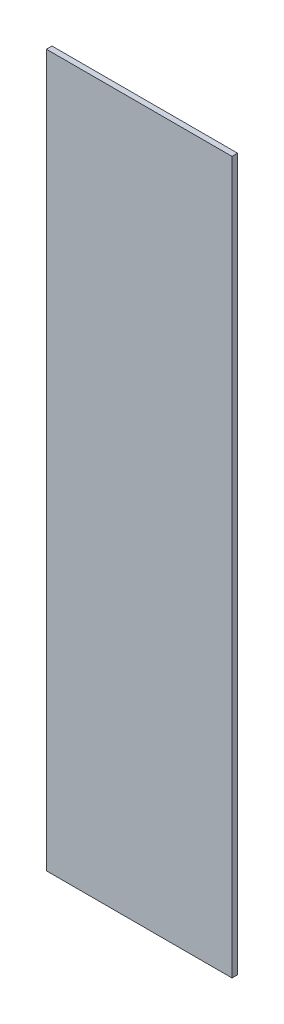
SolidWorks part; units mm, degrees
ref_plane "Спереди" through (0, 0, 0) normal (0, 0, 1) x (1, 0, 0)
ref_plane "Сверху" through (0, 0, 0) normal (0, 1, 0) x (1, 0, 0)
ref_plane "Справа" through (0, 0, 0) normal (1, 0, 0) x (0, 0, -1)
sketch "Эскиз1" plane through (0, 0, 0) normal (0, 0, 1) x (1, 0, 0)
  line L1 (0, 0) -> (600, 0)
  line L2 (0, 0) -> (0, 2300)
  line L3 (0, 2300) -> (600, 2300)
  line L4 (600, 0) -> (600, 2300)
  dimension "D1" = 600
  dimension "D2" = 2300
extrude "Бобышка-Вытянуть1" add sketch "Эскиз1" along normal blind 18
